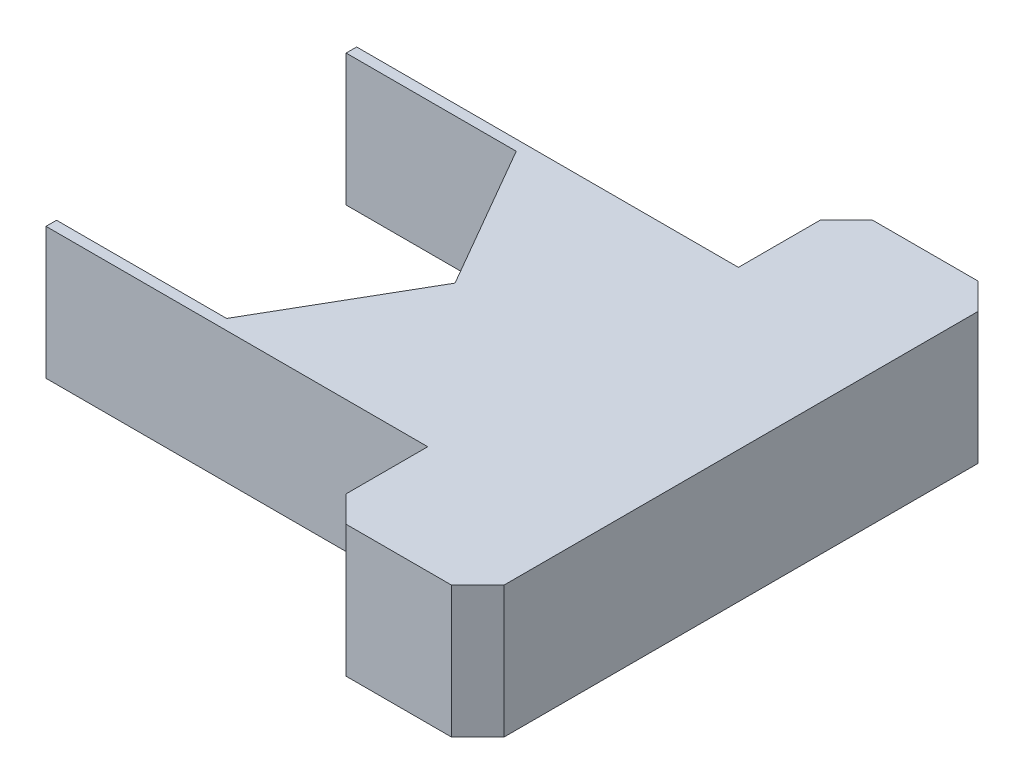
SolidWorks part; units mm, degrees
ref_plane "Front Plane" through (0, 0, 0) normal (0, 0, 1) x (1, 0, 0)
ref_plane "Top Plane" through (0, 0, 0) normal (0, 1, 0) x (1, 0, 0)
ref_plane "Right Plane" through (0, 0, 0) normal (1, 0, 0) x (0, 0, -1)
sketch "Sketch1" plane through (0, 0, 0) normal (0, 1, 0) x (1, 0, 0)
  line L0 (-1.5675, 2.95) -> (5.6825, 2.95)
  line L1 (3.135, 0) -> (1.5675, 2.715) construction
  line L2 (1.5675, 2.715) -> (-1.5675, 2.715) construction
  line L3 (-1.5675, 2.715) -> (-3.135, 0) construction
  line L4 (-3.135, 0) -> (-1.5675, -2.715) construction
  line L5 (-1.5675, -2.715) -> (1.5675, -2.715) construction
  line L6 (1.5675, -2.715) -> (3.135, 0) construction
  line L7 (5.6825, 2.95) -> (5.6825, -2.95)
  line L8 (5.6825, -2.95) -> (-1.5675, -2.95)
  line L9 (-1.5675, -2.95) -> (-1.5675, -2.75)
  line L10 (-1.5675, -2.75) -> (1.6628, -2.75)
  line L12 (1.6628, 2.75) -> (-1.5675, 2.75)
  line L13 (-1.5675, 2.75) -> (-1.5675, 2.95)
  line L14 (0, 0) -> (3.2505, 0) construction
  line L15 (1.6628, 2.75) -> (3.2505, 0)
  line L16 (3.2505, 0) -> (1.6628, -2.75)
  line L17 (3.2505, 0) -> (5.6825, 0) construction
  line L18 (8.6825, 0) -> (5.6825, 0) construction
  line L19 (5.6825, 5) -> (8.6825, 5)
  line L20 (5.6825, 5) -> (5.6825, -5)
  line L21 (5.6825, -5) -> (8.6825, -5)
  line L22 (8.6825, 5) -> (8.6825, -5)
  circle A0 centre (0, 0) radius 2.715 construction
  dimension "D1" = 5.43
  dimension "D2" = 0.2
  dimension "D3" = 7.25
  dimension "D4" = 5.9
  dimension "D5" = 0.1
  dimension "D6" = 10
  dimension "D7" = 3
extrude "Boss-Extrude1" add sketch "Sketch1" along normal blind 2.5 contours L15 L16 L10 L9 L8 L7 L0 L13 L12 | L22 L19 L20 L7 L21
chamfer "Chamfer1" distance 0.5 angle 45 4 edges at (8.6825, 1.25, 5) (5.6825, 1.25, 5) (8.6825, 1.25, -5) (5.6825, 1.25, -5)
